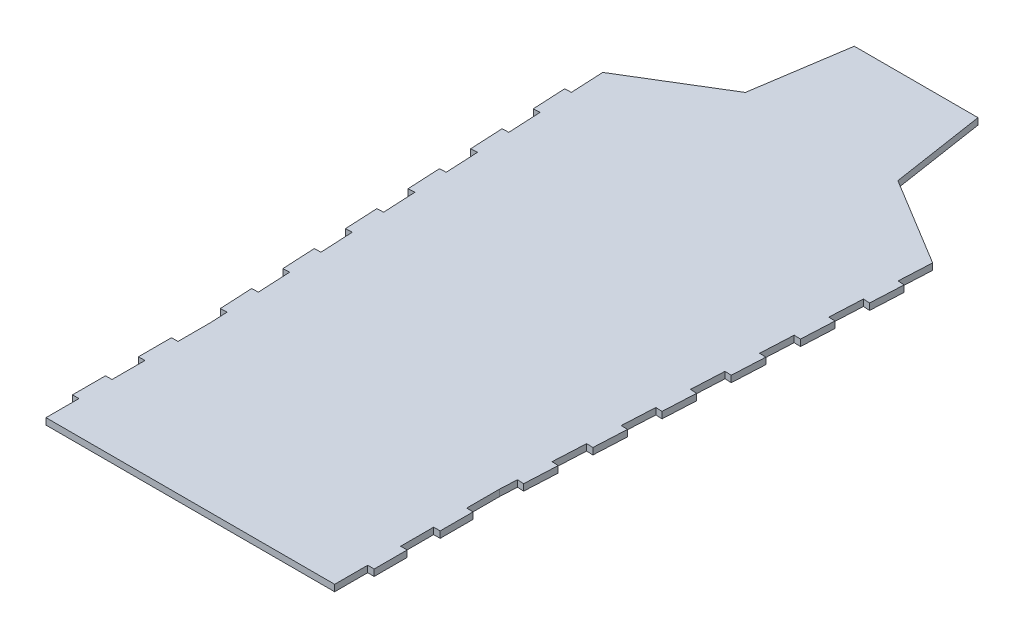
SolidWorks part; units mm, degrees
other "Markup1"
sketch "Sketch2" plane through (-261.64, 10, -187.9758) normal (0, 1, 0) x (1, 0, 0)
ref_plane "Front Plane" through (0, 0, 0) normal (0, 0, 1) x (1, 0, 0)
ref_plane "Top Plane" through (0, 0, 0) normal (0, 1, 0) x (1, 0, 0)
ref_plane "Right Plane" through (0, 0, 0) normal (1, 0, 0) x (0, 0, -1)
sketch "Sketch1" plane through (0, 0, 0) normal (0, 1, 0) x (1, 0, 0)
  line L11 (222.25, -751.8242) -> (254, -116.8242)
  line L12 (-254, -116.8242) -> (-222.25, -751.8242)
  line L13 (-222.25, -751.8242) -> (222.25, -751.8242)
  line L15 (-222.25, -751.8242) -> (222.25, -751.8242)
  line L16 (-222.25, -751.8242) -> (-222.25, -1005.8242)
  line L17 (-222.25, -1005.8242) -> (222.25, -1005.8242)
  line L18 (222.25, -751.8242) -> (222.25, -1005.8242)
  line L23 (0, -1005.8242) -> (0, 268.2158)
  line L24 (232.25, -904.2242) -> (232.25, -955.0242)
  line L27 (222.25, -955.0242) -> (232.25, -955.0242)
  line L28 (222.25, -904.2242) -> (222.25, -955.0242)
  line L29 (222.25, -904.2242) -> (232.25, -904.2242)
  line L30 (232.25, -802.6242) -> (232.25, -853.4242)
  line L31 (233.5456, -726.163) -> (223.558, -725.6637)
  line L32 (236.0824, -675.4264) -> (233.5456, -726.163)
  line L33 (226.0949, -674.927) -> (236.0824, -675.4264)
  line L34 (238.6192, -624.6898) -> (228.6317, -624.1904)
  line L35 (241.156, -573.9532) -> (238.6192, -624.6898)
  line L36 (231.1685, -573.4538) -> (241.156, -573.9532)
  line L37 (243.6929, -523.2166) -> (233.7054, -522.7172)
  line L38 (246.2297, -472.48) -> (243.6929, -523.2166)
  line L39 (236.2422, -471.9806) -> (246.2297, -472.48)
  line L40 (248.7665, -421.7433) -> (238.779, -421.244)
  line L41 (251.3034, -371.0067) -> (248.7665, -421.7433)
  line L42 (241.3158, -370.5073) -> (251.3034, -371.0067)
  line L43 (253.8402, -320.2701) -> (243.8527, -319.7707)
  line L45 (-222.25, -802.6242) -> (-232.25, -802.6242)
  line L46 (-222.25, -802.6242) -> (-222.25, -853.4242)
  line L47 (-222.25, -853.4242) -> (-232.25, -853.4242)
  line L48 (-251.4632, -167.5609) -> (-261.4507, -168.0602)
  line L49 (-261.4507, -168.0602) -> (-258.9139, -218.7969)
  line L50 (-258.9139, -218.7969) -> (-248.9263, -218.2975)
  line L51 (-246.3895, -269.0341) -> (-256.377, -269.5335)
  line L52 (-256.377, -269.5335) -> (-253.8402, -320.2701)
  line L53 (-253.8402, -320.2701) -> (-243.8527, -319.7707)
  line L54 (-241.3158, -370.5073) -> (-251.3034, -371.0067)
  line L55 (-251.3034, -371.0067) -> (-248.7665, -421.7433)
  line L56 (-248.7665, -421.7433) -> (-238.779, -421.244)
  line L57 (-236.2422, -471.9806) -> (-246.2297, -472.48)
  line L58 (-246.2297, -472.48) -> (-243.6929, -523.2166)
  line L59 (-243.6929, -523.2166) -> (-233.7054, -522.7172)
  line L60 (-231.1685, -573.4538) -> (-241.156, -573.9532)
  line L61 (-241.156, -573.9532) -> (-238.6192, -624.6898)
  line L62 (-238.6192, -624.6898) -> (-228.6317, -624.1904)
  line L63 (-226.0949, -674.927) -> (-236.0824, -675.4264)
  line L64 (-236.0824, -675.4264) -> (-233.5456, -726.163)
  line L65 (-233.5456, -726.163) -> (-223.558, -725.6637)
  line L66 (-232.25, -802.6242) -> (-232.25, -853.4242)
  line L67 (-222.25, -904.2242) -> (-232.25, -904.2242)
  line L68 (-222.25, -904.2242) -> (-222.25, -955.0242)
  line L69 (-222.25, -955.0242) -> (-232.25, -955.0242)
  line L70 (-232.25, -904.2242) -> (-232.25, -955.0242)
  line L71 (256.377, -269.5335) -> (253.8402, -320.2701)
  line L72 (246.3895, -269.0341) -> (256.377, -269.5335)
  line L73 (258.9139, -218.7969) -> (248.9263, -218.2975)
  line L74 (261.4507, -168.0602) -> (258.9139, -218.7969)
  line L75 (251.4632, -167.5609) -> (261.4507, -168.0602)
  line L76 (222.25, -853.4242) -> (232.25, -853.4242)
  line L77 (222.25, -802.6242) -> (222.25, -853.4242)
  line L78 (222.25, -802.6242) -> (232.25, -802.6242)
  line L79 (-254, -116.8242) -> (254, -116.8242)
  line L80 (-254, -116.8242) -> (-117.475, -33.7592)
  line L81 (-117.475, -33.7592) -> (-95.25, 111.7758)
  line L82 (-95.25, 111.7758) -> (0, 111.7758)
  line L83 (0, 111.7758) -> (95.25, 111.7758)
  line L84 (254, -116.8242) -> (117.602, -33.9576)
  line L85 (95.25, 111.7758) -> (117.602, -33.9576)
  point P18 (-238.125, -434.3242)
  point P79 (238.125, -434.3242)
  dimension "D2" = 508
  dimension "D3" = 87.138
  dimension "D6" = 95.25
  dimension "D7" = 117.475
  dimension "D8" = 228.6
  dimension "D9" = 130
  dimension "D10" = 117.602
  dimension "D11" = 31.75
  dimension "D12" = 95.25
  dimension "D13" = 635
  dimension "D14" = 254
  dimension "D15" = 50.8
  dimension "D16" = 10
  dimension "D17" = 50.8
  dimension "D18" = 50.8
  dimension "D19" = 50.8
  dimension "D20" = 10
  dimension "D21" = 130
  dimension "D40" = 10
  dimension "D41" = 50.8
  dimension "D42" = 50.8
  dimension "D43" = 10
  dimension "D44" = 50.8
  dimension "D45" = 50.8
  dimension "D46" = 10
  dimension "D47" = 50.8
  dimension "D48" = 50.8
  dimension "D49" = 50.8
  dimension "D50" = 50.8
  dimension "D51" = 10
  dimension "D52" = 50.8
  dimension "D53" = 50.8
  dimension "D54" = 10
  dimension "D55" = 50.8
  dimension "D56" = 10
  dimension "D57" = 50.8
extrude "Boss-Extrude1" add sketch "Sketch1" along normal blind 10
